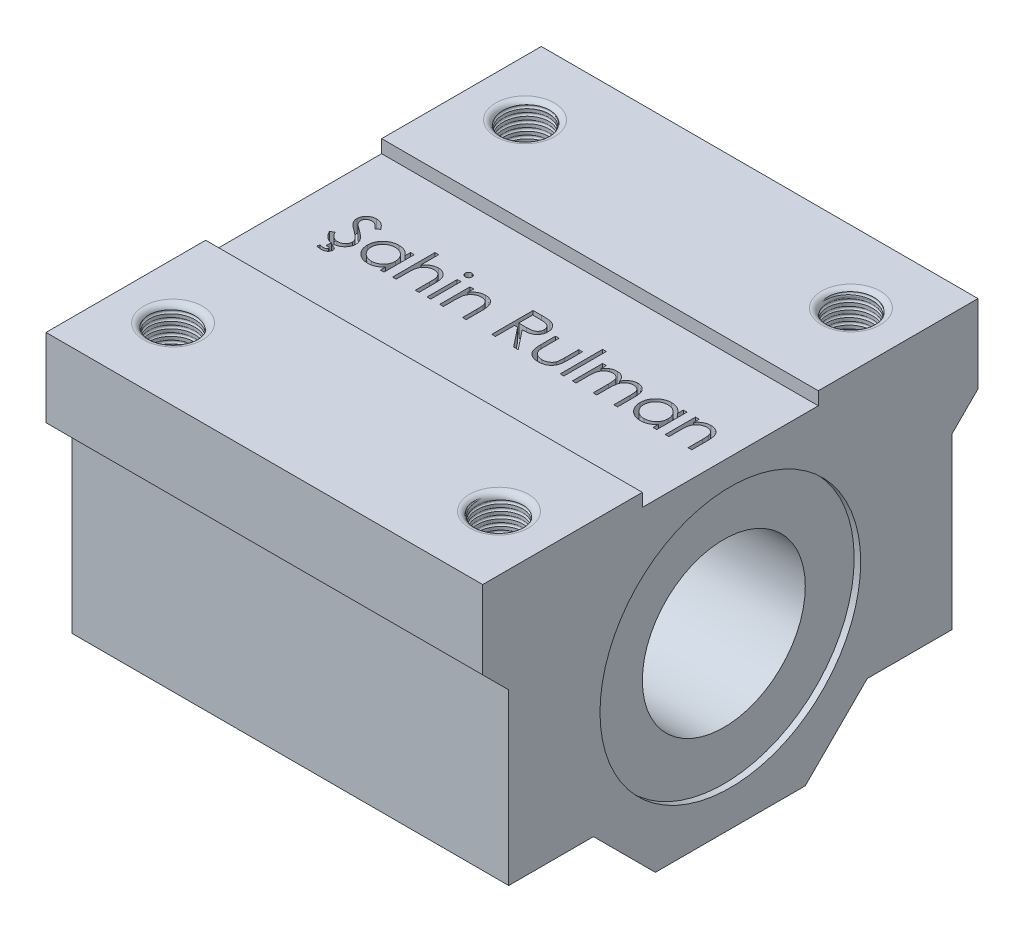
SolidWorks part; units mm, degrees
ref_plane "Front Plane" through (0, 0, 0) normal (0, 0, 1) x (1, 0, 0)
ref_plane "Top Plane" through (0, 0, 0) normal (0, 1, 0) x (1, 0, 0)
ref_plane "Right Plane" through (0, 0, 0) normal (1, 0, 0) x (0, 0, -1)
sketch "Sketch1" plane through (0, 0, 0) normal (1, 0, 0) x (0, 0, -1)
  line L0 (-38, 51.5) -> (-13.5, 51.5)
  line L1 (-38, 51.5) -> (-38, 39.5)
  line L2 (-38, 39.5) -> (-34, 35.5)
  line L3 (-34, 35.5) -> (-34, 9.5)
  line L4 (-34, 9.5) -> (-21, 9.5)
  line L5 (-21, 9.5) -> (-11.5, 0)
  line L6 (-11.5, 0) -> (11.5, 0)
  line L7 (0, 13) -> (0, 49.5) construction
  line L8 (21, 9.5) -> (11.5, 0)
  line L9 (34, 9.5) -> (21, 9.5)
  line L10 (34, 35.5) -> (34, 9.5)
  line L11 (38, 39.5) -> (34, 35.5)
  line L12 (38, 51.5) -> (38, 39.5)
  line L13 (13.5, 51.5) -> (38, 51.5)
  line L19 (-13.5, 49.5) -> (-13.5, 51.5)
  line L20 (13.5, 49.5) -> (13.5, 51.5)
  line L21 (-13.5, 49.5) -> (13.5, 49.5)
  circle A0 centre (0, 25.5) radius 12.5
  point P12 (0, 0)
  dimension "D10" = 25
  dimension "D1" = 51.5
  dimension "D2" = 42
  dimension "D3" = 4
  dimension "D4" = 4
  dimension "D5" = 12
  dimension "D6" = 38
  dimension "D7" = 13
  dimension "D8" = 76
  dimension "D9" = 26
  dimension "D17" = 2
extrude "Boss-Extrude1" add sketch "Sketch1" along normal mid plane 67
sketch "Sketch2" plane through (0, 51.5, 0) normal (0, 1, 0) x (1, 0, 0)
  circle A0 centre (-25, 27) radius 3.5
  circle A1 centre (25, 27) radius 3.5
  circle A2 centre (25, -27) radius 3.5
  circle A3 centre (-25, -27) radius 3.5
  dimension "D5" = 7
  dimension "D1" = 50
  dimension "D2" = 25
  dimension "D3" = 50
  dimension "D4" = 25
  dimension "D6" = 54
  dimension "D7" = 54
  dimension "D8" = 27
  dimension "D9" = 27
extrude "Cut-Extrude1" cut sketch "Sketch2" against normal through all
fillet "Fillet1" radius 1 4 edges at (-25, 51.5, -23.5) (25, 51.5, -23.5) (25, 51.5, 30.5) (-25, 51.5, 30.5)
sketch "Sketch3" plane through (0, 51.5, 0) normal (0, 1, 0) x (1, 0, 0)
  circle A0 centre (-25, -27) radius 3.5
curve "Helix/Spiral1" pitch 1 height 18 turns 18
ref_plane "Plane1" through (-27.4749, 0, 0) normal (-1, 0, 0) x (0, 0, 1)
sketch "Sketch4" plane through (-27.4749, 0, 0) normal (-1, 0, 0) x (0, 0, 1)
  circle A0 centre (24.5244, 51.5) radius 0.25
  spline S0 degree 3 poles (24.5251, 51.5) (24.2032, 51.4793) (23.6813, 51.4374) (23.4091, 51.375) (23.6822, 51.3125) (24.4607, 51.25) (25.6257, 51.1875) (27, 51.125) (28.3743, 51.0625) (29.5393, 51) (30.3178, 50.9375) (30.5911, 50.875) (30.3178, 50.8125) (29.5393, 50.75) (28.3743, 50.6875) (27, 50.625) (25.6257, 50.5625) (24.4607, 50.5) (23.6822, 50.4375) (23.4089, 50.375) (23.6822, 50.3125) (24.4607, 50.25) (25.6257, 50.1875) (27, 50.125) (28.3743, 50.0625) (29.5393, 50) (30.3178, 49.9375) (30.5911, 49.875) (30.3178, 49.8125) (29.5393, 49.75) (28.3743, 49.6875) (27, 49.625) (25.6257, 49.5625) (24.4607, 49.5) (23.6822, 49.4375) (23.4089, 49.375) (23.6822, 49.3125) (24.4607, 49.25) (25.6257, 49.1875) (27, 49.125) (28.3743, 49.0625) (29.5393, 49) (30.3178, 48.9375) (30.5911, 48.875) (30.3178, 48.8125) (29.5393, 48.75) (28.3743, 48.6875) (27, 48.625) (25.6257, 48.5625) (24.4607, 48.5) (23.6822, 48.4375) (23.4089, 48.375) (23.6822, 48.3125) (24.4607, 48.25) (25.6257, 48.1875) (27, 48.125) (28.3743, 48.0625) (29.5393, 48) (30.3178, 47.9375) (30.5911, 47.875) (30.3178, 47.8125) (29.5393, 47.75) (28.3743, 47.6875) (27, 47.625) (25.6257, 47.5625) (24.4607, 47.5) (23.6822, 47.4375) (23.4089, 47.375) (23.6822, 47.3125) (24.4607, 47.25) (25.6257, 47.1875) (27, 47.125) (28.3743, 47.0625) (29.5393, 47) (30.3178, 46.9375) (30.5911, 46.875) (30.3178, 46.8125) (29.5393, 46.75) (28.3743, 46.6875) (27, 46.625) (25.6257, 46.5625) (24.4607, 46.5) (23.6822, 46.4375) (23.4089, 46.375) (23.6822, 46.3125) (24.4607, 46.25) (25.6257, 46.1875) (27, 46.125) (28.3743, 46.0625) (29.5393, 46) (30.3178, 45.9375) (30.5911, 45.875) (30.3178, 45.8125) (29.5393, 45.75) (28.3743, 45.6875) (27, 45.625) (25.6257, 45.5625) (24.4607, 45.5) (23.6822, 45.4375) (23.4089, 45.375) (23.6822, 45.3125) (24.4607, 45.25) (25.6257, 45.1875) (27, 45.125) (28.3743, 45.0625) (29.5393, 45) (30.3178, 44.9375) (30.5911, 44.875) (30.3178, 44.8125) (29.5393, 44.75) (28.3743, 44.6875) (27, 44.625) (25.6257, 44.5625) (24.4607, 44.5) (23.6822, 44.4375) (23.4089, 44.375) (23.6822, 44.3125) (24.4607, 44.25) (25.6257, 44.1875) (27, 44.125) (28.3743, 44.0625) (29.5393, 44) (30.3178, 43.9375) (30.5911, 43.875) (30.3178, 43.8125) (29.5393, 43.75) (28.3743, 43.6875) (27, 43.625) (25.6257, 43.5625) (24.4607, 43.5) (23.6822, 43.4375) (23.4089, 43.375) (23.6822, 43.3125) (24.4607, 43.25) (25.6257, 43.1875) (27, 43.125) (28.3743, 43.0625) (29.5393, 43) (30.3178, 42.9375) (30.5911, 42.875) (30.3178, 42.8125) (29.5393, 42.75) (28.3743, 42.6875) (27, 42.625) (25.6257, 42.5625) (24.4607, 42.5) (23.6822, 42.4375) (23.4089, 42.375) (23.6822, 42.3125) (24.4607, 42.25) (25.6257, 42.1875) (27, 42.125) (28.3743, 42.0625) (29.5393, 42) (30.3178, 41.9375) (30.5911, 41.875) (30.3178, 41.8125) (29.5393, 41.75) (28.3743, 41.6875) (27, 41.625) (25.6257, 41.5625) (24.4607, 41.5) (23.6822, 41.4375) (23.4089, 41.375) (23.6822, 41.3125) (24.4607, 41.25) (25.6257, 41.1875) (27, 41.125) (28.3743, 41.0625) (29.5393, 41) (30.3178, 40.9375) (30.5911, 40.875) (30.3178, 40.8125) (29.5393, 40.75) (28.3743, 40.6875) (27, 40.625) (25.6257, 40.5625) (24.4607, 40.5) (23.6822, 40.4375) (23.4089, 40.375) (23.6822, 40.3125) (24.4607, 40.25) (25.6257, 40.1875) (27, 40.125) (28.3743, 40.0625) (29.5393, 40) (30.3178, 39.9375) (30.5911, 39.875) (30.3178, 39.8125) (29.5393, 39.75) (28.3743, 39.6875) (27, 39.625) (25.6257, 39.5625) (24.4607, 39.5) (23.6822, 39.4375) (23.4089, 39.375) (23.6822, 39.3125) (24.4607, 39.25) (25.6257, 39.1875) (27, 39.125) (28.3743, 39.0625) (29.5393, 39) (30.3178, 38.9375) (30.5911, 38.875) (30.3178, 38.8125) (29.5393, 38.75) (28.3743, 38.6875) (27, 38.625) (25.6257, 38.5625) (24.4607, 38.5) (23.6822, 38.4375) (23.4089, 38.375) (23.6822, 38.3125) (24.4607, 38.25) (25.6257, 38.1875) (27, 38.125) (28.3743, 38.0625) (29.5393, 38) (30.3178, 37.9375) (30.5911, 37.875) (30.3178, 37.8125) (29.5393, 37.75) (28.3743, 37.6875) (27, 37.625) (25.6257, 37.5625) (24.4607, 37.5) (23.6822, 37.4375) (23.4089, 37.375) (23.6822, 37.3125) (24.4607, 37.25) (25.6257, 37.1875) (27, 37.125) (28.3743, 37.0625) (29.5393, 37) (30.3178, 36.9375) (30.5911, 36.875) (30.3178, 36.8125) (29.5393, 36.75) (28.3743, 36.6875) (27, 36.625) (25.6257, 36.5625) (24.4607, 36.5) (23.6822, 36.4375) (23.4089, 36.375) (23.6822, 36.3125) (24.4607, 36.25) (25.6257, 36.1875) (27, 36.125) (28.3743, 36.0625) (29.5393, 36) (30.3178, 35.9375) (30.5911, 35.875) (30.3178, 35.8125) (29.5393, 35.75) (28.3743, 35.6875) (27, 35.625) (25.6257, 35.5625) (24.4607, 35.5) (23.6822, 35.4375) (23.4089, 35.375) (23.6822, 35.3125) (24.4607, 35.25) (25.6257, 35.1875) (27, 35.125) (28.3743, 35.0625) (29.5393, 35) (30.3178, 34.9375) (30.5911, 34.875) (30.3178, 34.8125) (29.5393, 34.75) (28.3743, 34.6875) (27, 34.625) (25.6257, 34.5625) (24.4607, 34.5) (23.6822, 34.4375) (23.4089, 34.375) (23.6822, 34.3125) (24.4607, 34.25) (25.6257, 34.1875) (27, 34.125) (28.3743, 34.0625) (29.5393, 34) (30.3178, 33.9375) (30.5911, 33.875) (30.3178, 33.8125) (29.5393, 33.75) (28.3743, 33.6875) (26.9997, 33.625) (25.6267, 33.5626) (24.847, 33.5207) (24.5251, 33.5) knots 0 0 0 0 0.003472 0.006944 0.010417 0.013889 0.017361 0.020833 0.024306 0.027778 0.03125 0.034722 0.038194 0.041667 0.045139 0.048611 0.052083 0.055556 0.059028 0.0625 0.065972 0.069444 0.072917 0.076389 0.079861 0.083333 0.086806 0.090278 0.09375 0.097222 0.100694 0.104167 0.107639 0.111111 0.114583 0.118056 0.121528 0.125 0.128472 0.131944 0.135417 0.138889 0.142361 0.145833 0.149306 0.152778 0.15625 0.159722 0.163194 0.166667 0.170139 0.173611 0.177083 0.180556 0.184028 0.1875 0.190972 0.194444 0.197917 0.201389 0.204861 0.208333 0.211806 0.215278 0.21875 0.222222 0.225694 0.229167 0.232639 0.236111 0.239583 0.243056 0.246528 0.25 0.253472 0.256944 0.260417 0.263889 0.267361 0.270833 0.274306 0.277778 0.28125 0.284722 0.288194 0.291667 0.295139 0.298611 0.302083 0.305556 0.309028 0.3125 0.315972 0.319444 0.322917 0.326389 0.329861 0.333333 0.336806 0.340278 0.34375 0.347222 0.350694 0.354167 0.357639 0.361111 0.364583 0.368056 0.371528 0.375 0.378472 0.381944 0.385417 0.388889 0.392361 0.395833 0.399306 0.402778 0.40625 0.409722 0.413194 0.416667 0.420139 0.423611 0.427083 0.430556 0.434028 0.4375 0.440972 0.444444 0.447917 0.451389 0.454861 0.458333 0.461806 0.465278 0.46875 0.472222 0.475694 0.479167 0.482639 0.486111 0.489583 0.493056 0.496528 0.5 0.503472 0.506944 0.510417 0.513889 0.517361 0.520833 0.524306 0.527778 0.53125 0.534722 0.538194 0.541667 0.545139 0.548611 0.552083 0.555556 0.559028 0.5625 0.565972 0.569444 0.572917 0.576389 0.579861 0.583333 0.586806 0.590278 0.59375 0.597222 0.600694 0.604167 0.607639 0.611111 0.614583 0.618056 0.621528 0.625 0.628472 0.631944 0.635417 0.638889 0.642361 0.645833 0.649306 0.652778 0.65625 0.659722 0.663194 0.666667 0.670139 0.673611 0.677083 0.680556 0.684028 0.6875 0.690972 0.694444 0.697917 0.701389 0.704861 0.708333 0.711806 0.715278 0.71875 0.722222 0.725694 0.729167 0.732639 0.736111 0.739583 0.743056 0.746528 0.75 0.753472 0.756944 0.760417 0.763889 0.767361 0.770833 0.774306 0.777778 0.78125 0.784722 0.788194 0.791667 0.795139 0.798611 0.802083 0.805556 0.809028 0.8125 0.815972 0.819444 0.822917 0.826389 0.829861 0.833333 0.836806 0.840278 0.84375 0.847222 0.850694 0.854167 0.857639 0.861111 0.864583 0.868056 0.871528 0.875 0.878472 0.881944 0.885417 0.888889 0.892361 0.895833 0.899306 0.902778 0.90625 0.909722 0.913194 0.916667 0.920139 0.923611 0.927083 0.930556 0.934028 0.9375 0.940972 0.944444 0.947917 0.951389 0.954861 0.958333 0.961806 0.965278 0.96875 0.972222 0.975694 0.979167 0.982639 0.986111 0.989583 0.993056 0.996528 1 1 1 1 construction
  dimension "D1" = 0.5
sweep "Cut-Sweep1" cut profiles "Sketch4" path "Helix/Spiral1"
mirror "Mirror1" about plane through (0, 0, 0) normal (0, 0, 1) of "Cut-Sweep1"
mirror "Mirror2" about plane through (0, 0, 0) normal (1, 0, 0) of "Mirror1", "Cut-Sweep1"
sketch "Sketch5" plane through (0, 49.5, 0) normal (0, 1, 0) x (1, 0, 0)
  text T0 "Şahin Rulman" font "Century Gothic" height in points 24
extrude "Cut-Extrude2" cut sketch "Sketch5" against normal blind 2
sketch "Sketch6" plane through (0, 0, -38) normal (0, 0, -1) x (-1, 0, 0)
  text T0 "SCE 25 UU" font "Century Gothic" height in points 20
extrude "Cut-Extrude3" cut sketch "Sketch6" against normal blind 2
sketch "Sketch7" plane through (-33.5, 0, 0) normal (-1, 0, 0) x (0, 0, 1)
  circle A0 centre (0, 25.5) radius 20
  dimension "D1" = 40
extrude "Cut-Extrude4" cut sketch "Sketch7" against normal blind 1
mirror "Mirror3" about plane through (0, 0, 0) normal (1, 0, 0) of "Cut-Extrude4"
